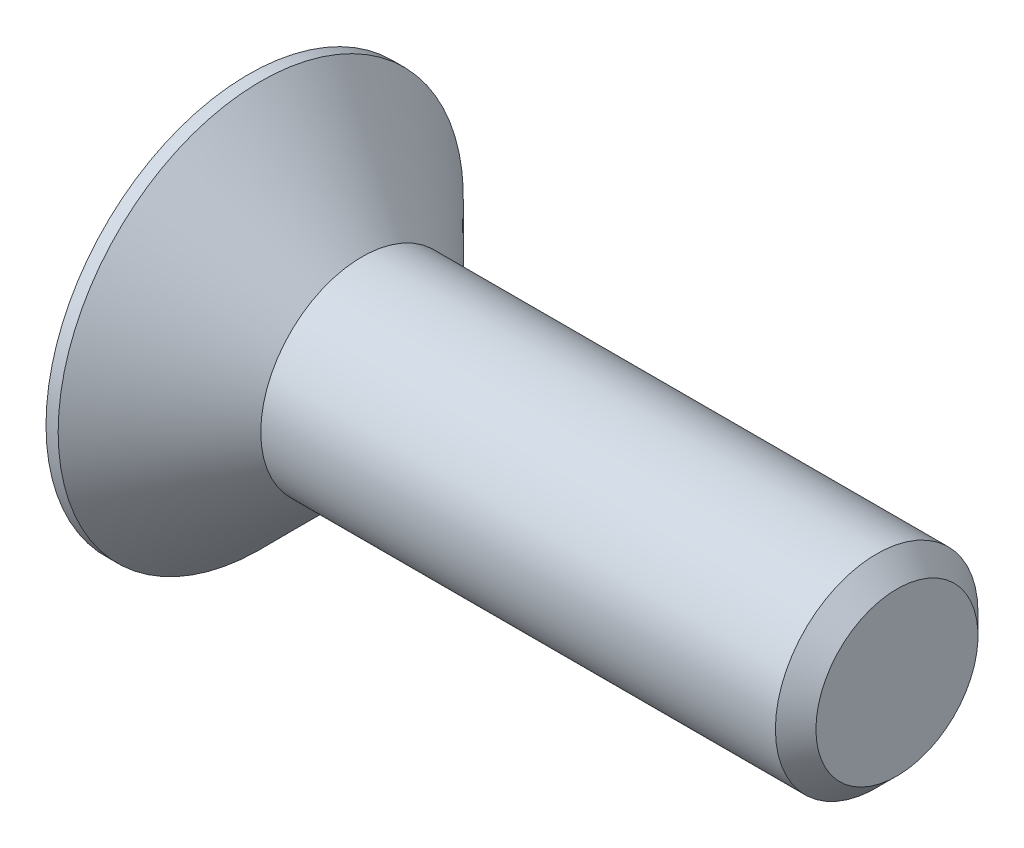
SolidWorks part; units mm, degrees
ref_plane "Front Plane" through (0, 0, 0) normal (0, 0, 1) x (1, 0, 0)
ref_plane "Top Plane" through (0, 0, 0) normal (0, 1, 0) x (1, 0, 0)
ref_plane "Right Plane" through (0, 0, 0) normal (1, 0, 0) x (0, 0, -1)
sketch "Sketch2" plane through (0, 0, 0) normal (0, 0, 1) x (1, 0, 0)
  line L0 (0, 0) -> (0, 2.5)
  line L1 (0, 2.5) -> (0.15, 2.5)
  line L2 (0.15, 2.5) -> (1.4, 1.25)
  line L3 (1.4, 1.25) -> (7.75, 1.25)
  line L4 (7.75, 1.25) -> (8, 1)
  line L5 (8, 1) -> (8, 0)
  line L6 (8, 0) -> (0, 0)
  line L7 (-2.2818, 0) -> (8.0811, 0) construction
  dimension "D1" = 5
  dimension "D2" = 0.15
  dimension "D3" = 45
  dimension "D4" = 8
  dimension "D5" = 0.25
  dimension "D6" = 2.5
revolve "Revolve1" add sketch "Sketch2" angle 360 about L7
sketch "Sketch3" plane through (0, 0, 0) normal (-1, 0, 0) x (0, 0, 1)
  line L1 (0.433, -0.75) -> (0.866, 0)
  line L2 (0.866, 0) -> (0.433, 0.75)
  line L3 (0.433, 0.75) -> (-0.433, 0.75)
  line L4 (-0.433, 0.75) -> (-0.866, 0)
  line L5 (-0.866, 0) -> (-0.433, -0.75)
  line L6 (-0.433, -0.75) -> (0.433, -0.75)
  circle A0 centre (0, 0) radius 0.75 construction
  dimension "D1" = 1.5
extrude "Cut-Extrude1" cut sketch "Sketch3" against normal blind 0.8
